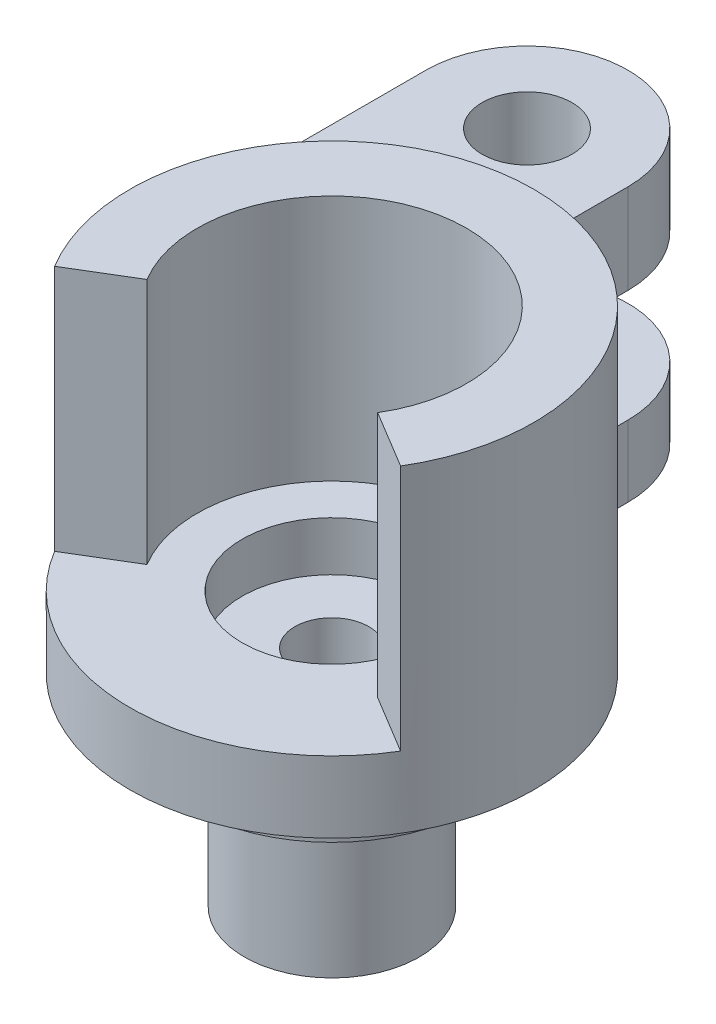
SolidWorks part; units mm, degrees
ref_plane "Front Plane" through (0, 0, 0) normal (0, 0, 1) x (1, 0, 0)
ref_plane "Top Plane" through (0, 0, 0) normal (0, 1, 0) x (1, 0, 0)
ref_plane "Right Plane" through (0, 0, 0) normal (1, 0, 0) x (0, 0, -1)
sketch "Sketch1" plane through (0, 0, 0) normal (0, 1, 0) x (1, 0, 0)
  circle A0 centre (0, 0) radius 9
  dimension "D1" = 18
extrude "Boss-Extrude1" add sketch "Sketch1" along normal blind 3.175
sketch "Sketch2" plane through (0, 3.175, 0) normal (0, 1, 0) x (1, 0, 0)
  line L0 (-7.7077, -4.6466) -> (-5.1385, -3.0978)
  line L1 (-7.7077, -4.6466) -> (7.7077, -4.6466) construction
  line L3 (5.1385, -3.0978) -> (7.7077, -4.6466)
  arc A0 (-7.7077, -4.6466) -> (7.7077, -4.6466) centre (0, 0) cw
  circle A1 centre (0, 0) radius 9 construction
  arc A2 (-5.1385, -3.0978) -> (5.1385, -3.0978) centre (0, 0) cw
  dimension "D1" = 117.832
  dimension "D2" = 3
extrude "Boss-Extrude2" add sketch "Sketch2" along normal blind 11
sketch "Sketch3" plane through (0, 0, 0) normal (0, -1, 0) x (1, 0, 0)
  circle A0 centre (0, 0) radius 6.4
  dimension "D1" = 12.8
extrude "Boss-Extrude3" add sketch "Sketch3" along normal blind 2
sketch "Sketch4" plane through (0, -2, 0) normal (0, -1, 0) x (1, 0, 0)
  circle A0 centre (0, 0) radius 3.9
  dimension "D1" = 7.8
extrude "Boss-Extrude4" add sketch "Sketch4" along normal blind 7
sketch "Sketch6" plane through (0, 0, 0) normal (0, 1, 0) x (1, 0, 0)
  line L0 (-9, 0) -> (-9, 13.1942)
  line L1 (0, 9) -> (0, 13.1942)
  arc A0 (7.7077, -4.6466) -> (-7.7077, -4.6466) centre (0, 0) ccw construction
  arc A1 (0, 13.1942) -> (-9, 13.1942) centre (-4.5, 13.1942) ccw
  arc A2 (0, 9) -> (-9, 0) centre (0, 0) ccw
  point P10 (-4.5, 17.6942)
  dimension "D1" = 8.6942
extrude "Boss-Extrude5" add sketch "Sketch6" along normal up to surface (3.175 mm away) up to face at (0, 3.175, 2.6861)
ref_plane "Plane1" through (0, 8.175, 0) normal (0, 1, 0) x (1, 0, 0)
sketch "Sketch7" plane through (0, 8.175, 0) normal (0, 1, 0) x (1, 0, 0)
  line L0 (0, 9) -> (0, 13.1942) construction
  line L1 (-9, 13.1942) -> (-9, 0) construction
  line L2 (0, 9) -> (0, 13.1942)
  line L3 (-9, 13.1942) -> (-9, 0)
  arc A0 (0, 9) -> (-9, 0) centre (0, 0) ccw construction
  arc A1 (0, 13.1942) -> (-9, 13.1942) centre (-4.5, 13.1942) ccw construction
  arc A2 (0, 9) -> (-9, 0) centre (0, 0) ccw
  arc A3 (0, 13.1942) -> (-9, 13.1942) centre (-4.5, 13.1942) ccw
extrude "Boss-Extrude7" add sketch "Sketch7" along normal blind 4
sketch "Sketch8" plane through (0, 12.175, 0) normal (0, 1, 0) x (1, 0, 0)
  circle A0 centre (-4.5, 13.1942) radius 2
  arc A1 (0, 13.1942) -> (-9, 13.1942) centre (-4.5, 13.1942) ccw construction
  dimension "D1" = 4
extrude "Cut-Extrude1" cut sketch "Sketch8" against normal up to surface (4 mm away) up to face at (-4.966, 8.175, -10.4381)
sketch "Sketch9" plane through (0, 3.175, 0) normal (0, 1, 0) x (1, 0, 0)
  circle A0 centre (0, 0) radius 1.65
  dimension "D1" = 3.3
extrude "Cut-Extrude2" cut sketch "Sketch9" against normal up to surface (12.175 mm away) contours A0 up to face at (0, -9, -3.9)
sketch "Sketch10" plane through (0, 3.175, 0) normal (0, 1, 0) x (1, 0, 0)
  circle A0 centre (0, 0) radius 4
  dimension "D1" = 8
extrude "Cut-Extrude3" cut sketch "Sketch10" against normal blind 2.2
sketch "Sketch11" plane through (0, 3.175, 0) normal (0, 1, 0) x (1, 0, 0)
  circle A0 centre (-4.5, 13.1942) radius 1.7145
  dimension "D1" = 3.429
extrude "Cut-Extrude4" cut sketch "Sketch11" against normal blind 1.5
